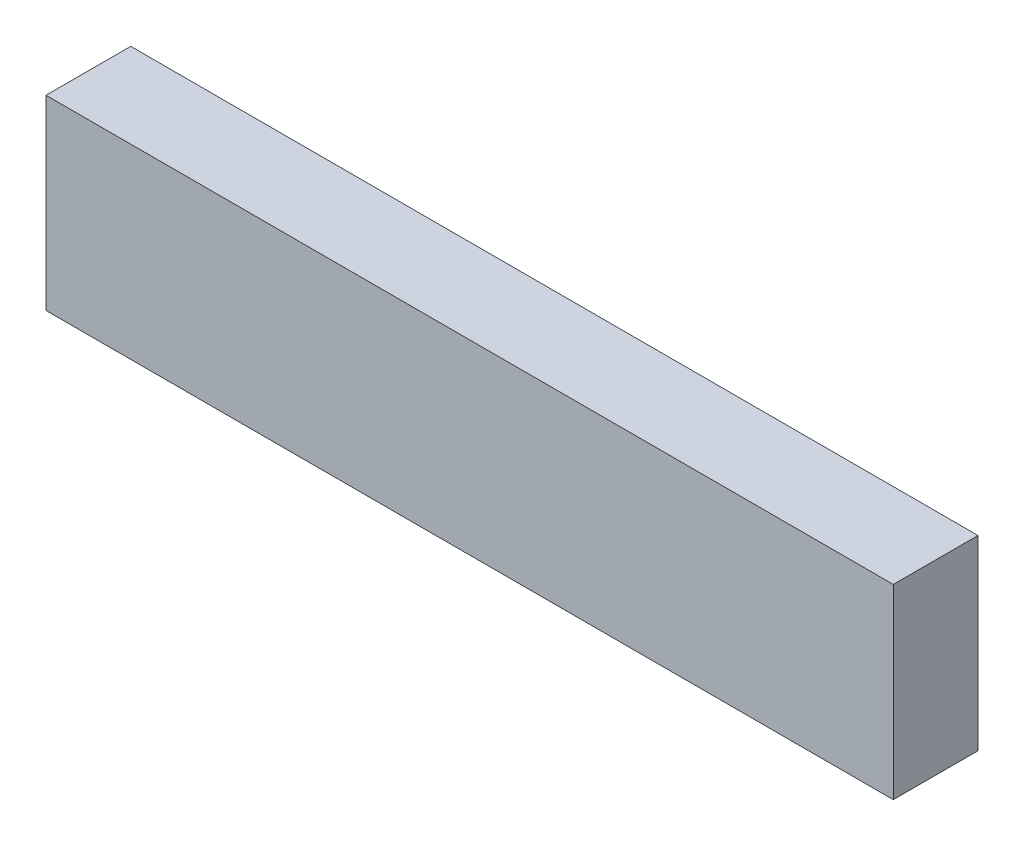
SolidWorks part; units mm, degrees
ref_plane "Front Plane" through (0, 0, 0) normal (0, 0, 1) x (1, 0, 0)
ref_plane "Top Plane" through (0, 0, 0) normal (0, 1, 0) x (1, 0, 0)
ref_plane "Right Plane" through (0, 0, 0) normal (1, 0, 0) x (0, 0, -1)
sketch "Sketch1" plane through (0, 0, 0) normal (0, 0, 1) x (1, 0, 0)
  line L1 (0, 0) -> (-100, 0)
  line L2 (0, 0) -> (0, 22)
  line L3 (0, 22) -> (-100, 22)
  line L4 (-100, 0) -> (-100, 22)
  dimension "D1" = 100
  dimension "D2" = 22
extrude "Boss-Extrude1" add sketch "Sketch1" along normal blind 10
